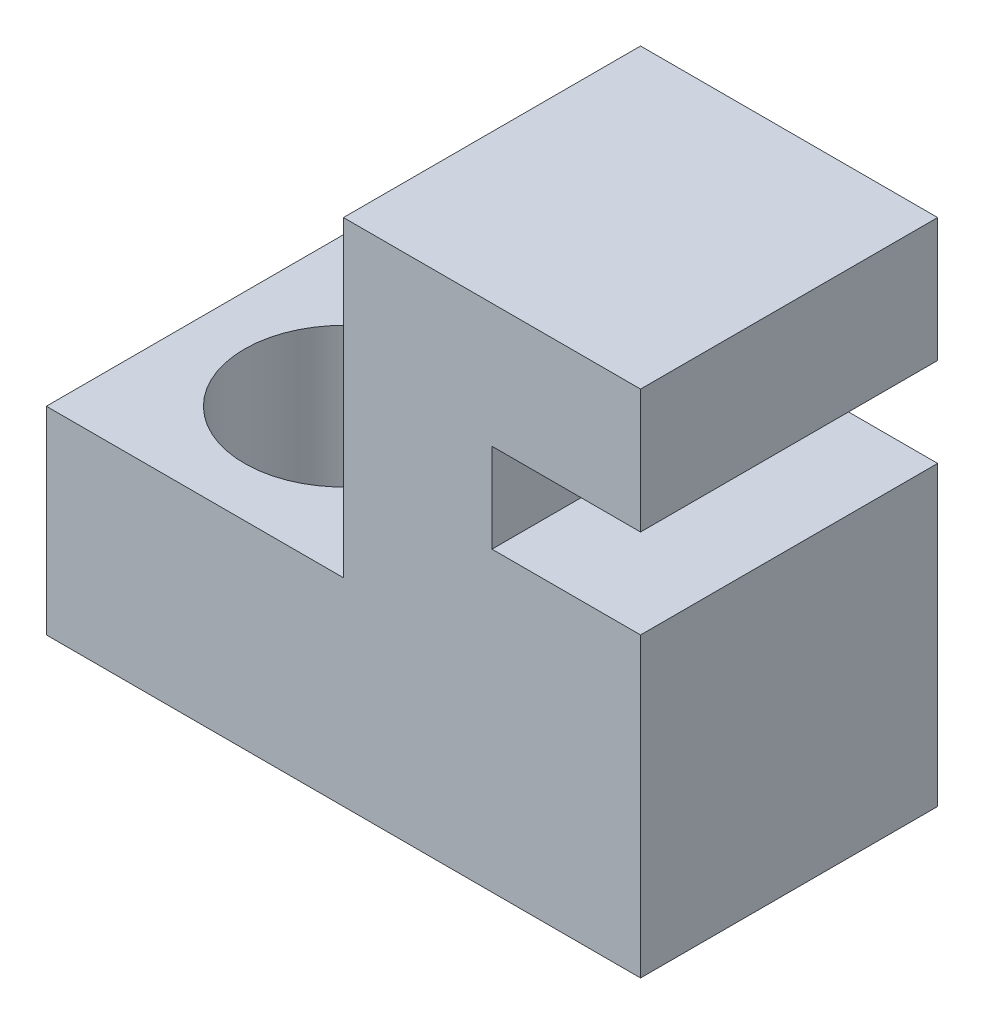
SolidWorks part; units mm, degrees
ref_plane "Спереди" through (0, 0, 0) normal (0, 0, 1) x (1, 0, 0)
ref_plane "Сверху" through (0, 0, 0) normal (0, 1, 0) x (1, 0, 0)
ref_plane "Справа" through (0, 0, 0) normal (1, 0, 0) x (0, 0, -1)
sketch "Эскиз1" plane through (0, 0, 0) normal (0, 0, 1) x (1, 0, 0)
  line L0 (0, 0) -> (0, 4)
  line L1 (0, 4) -> (6, 4)
  line L2 (6, 4) -> (6, 10.3)
  line L3 (6, 10.3) -> (12, 10.3)
  line L4 (12, 10.3) -> (12, 7.8)
  line L5 (12, 7.8) -> (9, 7.8)
  line L6 (9, 7.8) -> (9, 6)
  line L7 (9, 6) -> (12, 6)
  line L8 (12, 6) -> (12, 0)
  line L9 (12, 0) -> (0, 0)
  point P3 (9, 10.3)
  dimension "D1" = 1.8
  dimension "D2" = 3
  dimension "D3" = 6
  dimension "D4" = 4
  dimension "D5" = 2.5
  dimension "D6" = 6
  dimension "D7" = 6
extrude "Бобышка-Вытянуть1" add sketch "Эскиз1" along normal blind 6
sketch "Эскиз2" plane through (0, 4, 0) normal (0, 1, 0) x (1, 0, 0)
  line L0 (3, 0) -> (3, -6) construction
  line L1 (6, 0) -> (0, 0) construction
  line L2 (6, -6) -> (0, -6) construction
  circle A0 centre (3, -3) radius 2
  dimension "D1" = 4
extrude "Вырез-Вытянуть1" cut sketch "Эскиз2" against normal through all
